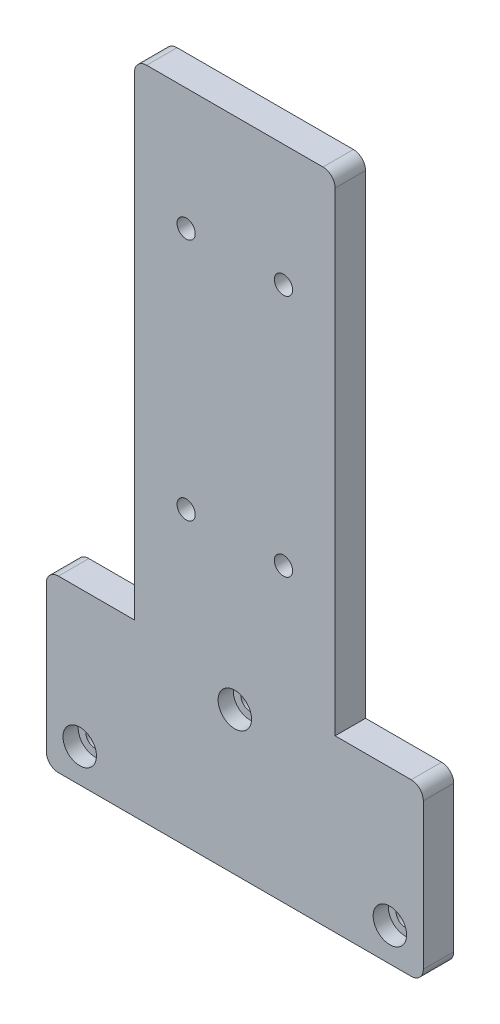
SolidWorks part; units mm, degrees
ref_plane "Front Plane" through (0, 0, 0) normal (0, 0, 1) x (1, 0, 0)
ref_plane "Top Plane" through (0, 0, 0) normal (0, 1, 0) x (1, 0, 0)
ref_plane "Right Plane" through (0, 0, 0) normal (1, 0, 0) x (0, 0, -1)
sketch "Sketch2" plane through (0, 0, 0) normal (0, 0, 1) x (1, 0, 0)
  line L0 (-31, 0) -> (-31, 28)
  line L1 (34.1, 0) -> (-34.1, 0) construction
  line L2 (-31, 28) -> (-16.5, 28)
  line L3 (-16.5, 28) -> (-16.5, 108)
  line L4 (-16.5, 108) -> (16.5, 108)
  line L5 (16.5, 108) -> (16.5, 28)
  line L6 (16.5, 28) -> (31, 28)
  line L7 (31, 28) -> (31, 0)
  line L8 (31, 0) -> (-31, 0)
  line L9 (0, 108) -> (0, 0) construction
  point P4 (0, 0)
  dimension "D1" = 33
  dimension "D2" = 80
  dimension "D3" = 62
  dimension "D4" = 28
extrude "Boss-Extrude1" add sketch "Sketch2" along normal blind 5
hole_wizard "Hole1" positions "Sketch5" profile "Sketch6" legacy end condition through all
sketch "Sketch5" plane through (0, 0, 5) normal (0, 0, 1) x (1, 0, 0)
  line L0 (0, 108) -> (0, 0) construction
  line L1 (-31, 28) -> (-31, 0) construction
  line L2 (-31, 0) -> (31, 0) construction
  point P0 (-25.5, 5.5)
  point P2 (25.5, 5.5)
  point P4 (0, 23.5)
  dimension "D1" = 51
  dimension "D2" = 5.5
  dimension "D3" = 5.5
  dimension "D4" = 18
sketch "Sketch6" plane through (-25.5, 5.5, 5) normal (1, 0, 0) x (0, -1, 0)
  line L0 (0, 0) -> (0, 5)
  line L1 (0, 5) -> (1.5, 5)
  line L2 (1.5, 5) -> (1.5, 2.5)
  line L3 (1.5, 2.5) -> (2.75, 2.5)
  line L4 (2.75, 2.5) -> (2.75, 0)
  line L5 (2.75, 0) -> (0, 0)
  line L6 (0, 110) -> (0, -10) construction
  dimension "Diameter" = 3
  dimension "Depth" = 5
  dimension "C-Bore Diameter" = 5.5
  dimension "C-Bore Depth" = 2.5
hole_wizard "Hole2" positions "Sketch7" profile "Sketch8" legacy end condition through all
sketch "Sketch7" plane through (0, 0, 0) normal (0, 0, 1) x (1, 0, 0)
  line L0 (-8, 88) -> (8, 88) construction
  line L1 (8, 88) -> (8, 48) construction
  line L2 (8, 48) -> (-8, 48) construction
  line L3 (-8, 48) -> (-8, 88) construction
  line L6 (0, 108) -> (0, 0) construction
  line L8 (-16.5, 108) -> (16.5, 108) construction
  point P0 (8, 48)
  point P2 (-8, 48)
  point P4 (-8, 88)
  point P6 (8, 88)
  point P21 (0, 48)
  dimension "D1" = 20
  dimension "D2" = 40
  dimension "D3" = 16
sketch "Sketch8" plane through (8, 48, 0) normal (1, 0, 0) x (0, 1, 0)
  line L0 (0, 0) -> (0, 5)
  line L1 (0, 5) -> (1.5, 5)
  line L2 (1.5, 5) -> (1.5, 2.5)
  line L3 (1.5, 2.5) -> (2.75, 2.5)
  line L4 (2.75, 2.5) -> (2.75, 0)
  line L5 (2.75, 0) -> (0, 0)
  line L6 (0, 110) -> (0, -10) construction
  dimension "Diameter" = 3
  dimension "Depth" = 5
  dimension "C-Bore Diameter" = 5.5
  dimension "C-Bore Depth" = 2.5
fillet "Fillet1" radius 2 6 edges at (-16.5, 108, 2.5) (16.5, 108, 2.5) (31, 28, 2.5) (31, 0, 2.5) (-31, 0, 2.5) (-31, 28, 2.5)
sketch "Sketch9" plane through (0, 0, 5) normal (0, 0, 1) x (1, 0, 0)
  line L1 (-16.5, 28) -> (-21.5, 28)
  line L2 (-16.5, 28) -> (-16.5, 18)
  line L3 (-16.5, 18) -> (-21.5, 18)
  line L4 (-21.5, 28) -> (-21.5, 18)
  dimension "D1" = 10
  dimension "D2" = 5
extrude "Boss-Extrude2" [suppressed] add sketch "Sketch9" along normal blind 5
fillet "Fillet2" [suppressed] radius 2
mirror "Mirror1" [suppressed] about plane through (0, 0, 0) normal (1, 0, 0)
